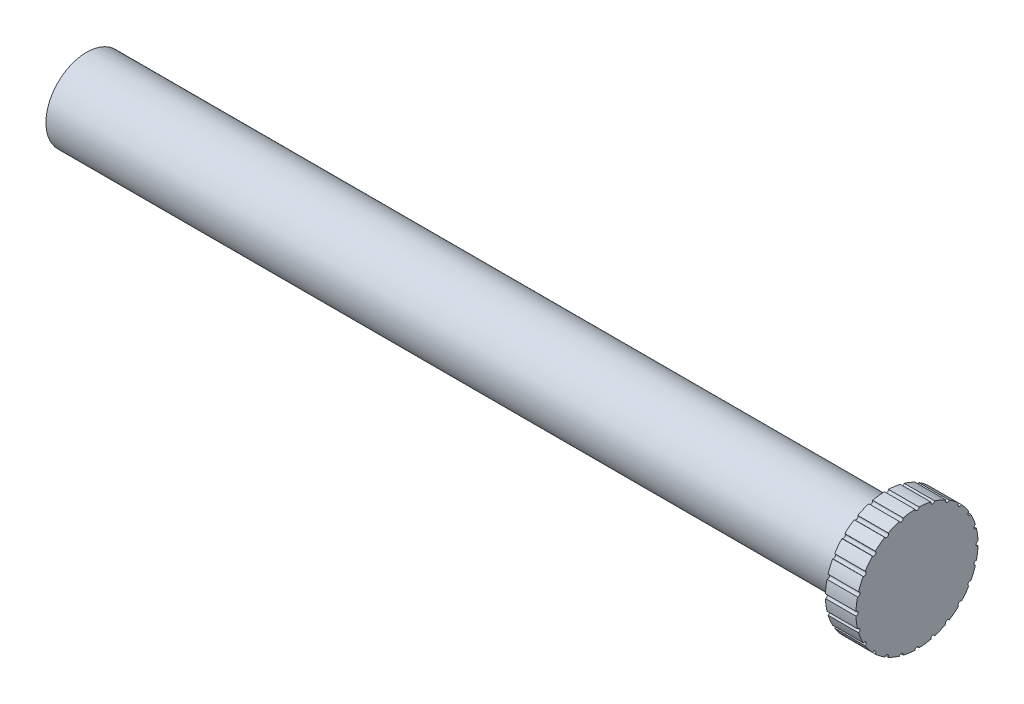
SolidWorks part; units mm, degrees
ref_plane "Ön Düzlem" through (0, 0, 0) normal (0, 0, 1) x (1, 0, 0)
ref_plane "Üst Düzlem" through (0, 0, 0) normal (0, 1, 0) x (1, 0, 0)
ref_plane "Sağ Düzlem" through (0, 0, 0) normal (1, 0, 0) x (0, 0, -1)
sketch "Sketch1" plane through (0, 0, 0) normal (1, 0, 0) x (0, 0, -1)
  circle A0 centre (0, 0) radius 4
  dimension "D1" = 8
extrude "Boss-Extrude1" add sketch "Sketch1" along normal blind 78.63
sketch "Sketch2" plane through (78.63, 0, 0) normal (1, 0, 0) x (0, 0, -1)
  circle A0 centre (0, 0) radius 6
extrude "Boss-Extrude2" add sketch "Sketch2" along normal blind 3
sketch "Sketch3" plane through (81.63, 0, 0) normal (1, 0, 0) x (0, 0, -1)
  circle A0 centre (-6, 0) radius 0.2
  circle A1 centre (0, 0) radius 6 construction
extrude "Cut-Extrude1" cut sketch "Sketch3" against normal up to surface (3 mm away) up to face at (78.63, 0, -4)
pattern_circular "CirPattern1" count 25 every 15 about axis through (0, 0, 0) along (1, 0, 0) of "Cut-Extrude1"
